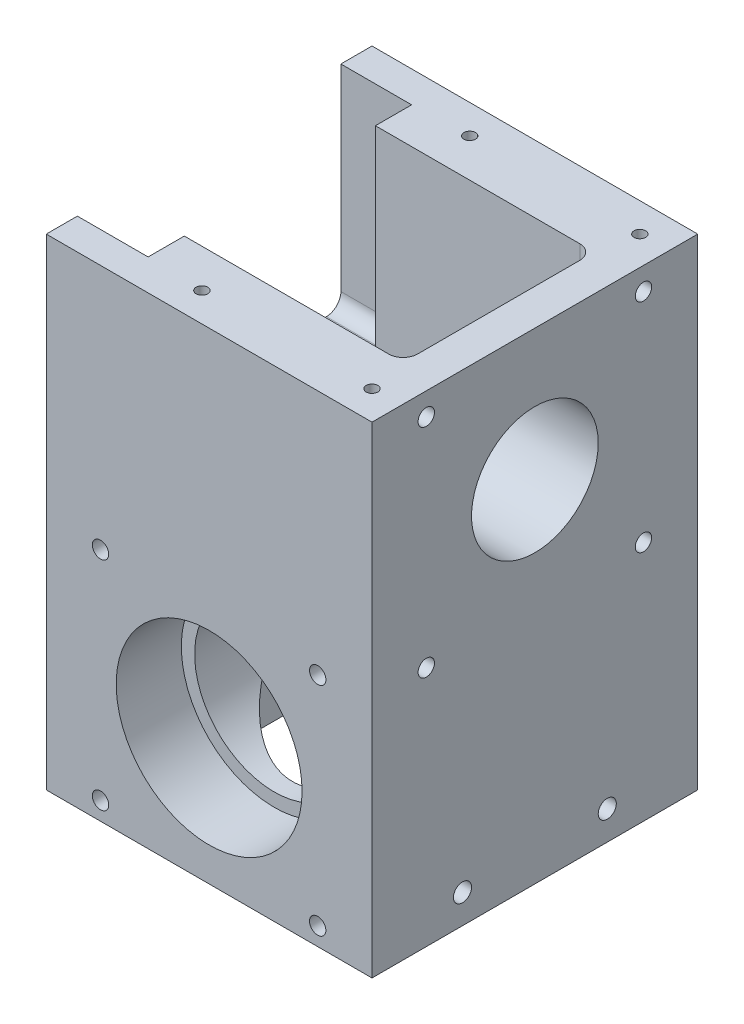
SolidWorks part; units mm, degrees
ref_plane "Front Plane" through (0, 0, 0) normal (0, 0, 1) x (1, 0, 0)
ref_plane "Top Plane" through (0, 0, 0) normal (0, 1, 0) x (1, 0, 0)
ref_plane "Right Plane" through (0, 0, 0) normal (1, 0, 0) x (0, 0, -1)
sketch "Sketch1" plane through (0, 0, 0) normal (0, 1, 0) x (1, 0, 0)
  line L1 (-22.5, -22.5) -> (22.5, -22.5)
  line L2 (-22.5, -22.5) -> (-22.5, 22.5)
  line L3 (-22.5, 22.5) -> (22.5, 22.5)
  line L4 (22.5, -22.5) -> (22.5, 22.5)
  line L5 (-22.5, -22.5) -> (22.5, 22.5) construction
  line L6 (-22.5, 22.5) -> (22.5, -22.5) construction
  point P0 (0, 0)
  dimension "D1" = 45
extrude "Boss-Extrude1" add sketch "Sketch1" along normal blind 30 and the other way blind 35
ref_plane "Plane1" through (0, 15, 0) normal (0, 1, 0) x (1, 0, 0)
ref_plane "Plane2" through (0, -17.5, 0) normal (0, -1, 0) x (-1, 0, 0)
hole_wizard "Ø22.0 (22) Diameter Hole1" positions "Sketch3" profile "Sketch4" hole size "Ø22.0" standard "DIN" end condition through all
sketch "Sketch3" plane through (0, 30, 0) normal (0, 1, 0) x (1, 0, 0)
  point P0 (0, 0)
sketch "Sketch4" plane through (0, 30, 0) normal (1, 0, 0) x (0, 0, 1)
  line L0 (0, 0) -> (0, 65)
  line L1 (0, 65) -> (11, 65)
  line L2 (11, 65) -> (11, 0)
  line L5 (11, 0) -> (0, 0)
  line L11 (0, -6.35) -> (0, 107.95) construction
  dimension "Thru Hole Dia." = 22
  dimension "Thru Hole Depth" = 65
hole_wizard "Ø22.0 (22) Diameter Hole2" positions "Sketch5" profile "Sketch6" hole size "Ø22.0" standard "DIN" end condition through all
sketch "Sketch5" plane through (0, 0, 22.5) normal (0, 0, 1) x (1, 0, 0)
  line L0 (-24.75, -17.5) -> (24.75, -17.5) construction
  point P0 (0, -17.5)
sketch "Sketch6" plane through (0, -17.5, 22.5) normal (1, 0, 0) x (0, -1, 0)
  line L0 (0, 0) -> (0, 45)
  line L1 (0, 45) -> (11, 45)
  line L2 (11, 45) -> (11, 0)
  line L5 (11, 0) -> (0, 0)
  line L11 (0, -6.35) -> (0, 107.95) construction
  dimension "Thru Hole Dia." = 22
  dimension "Thru Hole Depth" = 45
sketch "Sketch7" plane through (0, 0, 22.5) normal (0, 0, 1) x (1, 0, 0)
  circle A0 centre (0, -17.5) radius 12.8397
  dimension "D1" = 25.6794
extrude "Cut-Extrude1" cut sketch "Sketch7" against normal blind 9
cosmetic thread "Cosmetic Thread1" parameters "D1"=5, "D2"=26.289
sketch "Sketch8" plane through (0, 0, 0) normal (0, 0, 1) x (1, 0, 0)
  line L0 (-12.7279, 2.2721) -> (-11.9147, 1.4589)
  line L1 (-11.9147, 1.4589) -> (13.5411, 26.9147)
  line L2 (13.5411, 26.9147) -> (12.7279, 27.7279)
  line L3 (12.7279, 27.7279) -> (-12.7279, 2.2721)
  line L4 (24.75, 15) -> (-24.75, 15) construction
  point P2 (0, 15)
  dimension "D1" = 1.15
  dimension "D2" = 36
  dimension "D3" = 45
extrude "Cut-Extrude2" cut sketch "Sketch8" against normal mid plane 26.4
sketch "Sketch9" plane through (-6.6868, 6.6868, 0) normal (-0.7071, 0.7071, 0) x (0, 0, 1)
  line L4 (13.2, -7.3934) -> (13.2, 28.6066)
  line L5 (13.2, 28.6066) -> (-13.2, 28.6066)
  line L6 (-13.2, 28.6066) -> (-13.2, -7.3934)
  line L7 (-13.2, -7.3934) -> (13.2, -7.3934)
  line L8 (13.2, -7.3934) -> (13.2, 28.6066)
  line L9 (13.2, 28.6066) -> (-13.2, 28.6066)
  line L10 (-13.2, 28.6066) -> (-13.2, -7.3934)
  line L11 (-13.2, -7.3934) -> (13.2, -7.3934)
  dimension "D1" = 0
extrude "Cut-Extrude3" cut sketch "Sketch9" along normal up to next
fillet "Fillet1" radius 2 4 edges at (-17.2074, 6.7515, 13.2) (-17.2074, 6.7515, -13.2) (11.9985, 28.4574, 13.2) (11.9985, 28.4574, -13.2)
sketch "Sketch12" plane through (-6.6868, 6.6868, 0) normal (-0.7071, 0.7071, 0) x (0, 0, 1)
  line L0 (-11.2, -5.3934) -> (-11.2, -7.3934) construction
  line L1 (-9.2, -5.3934) -> (-9.2, -7.3934)
  line L2 (-13.2, -5.3934) -> (-13.2, -7.3934)
  line L4 (11.2, -5.3934) -> (11.2, -7.3934) construction
  line L5 (13.2, -5.3934) -> (13.2, -7.3934)
  line L6 (9.2, -5.3934) -> (9.2, -7.3934)
  line L7 (-11.2, -7.3934) -> (11.2, -7.3934) construction
  line L8 (-11.2, -7.3934) -> (11.2, -7.3934) construction
  arc A0 (-9.2, -5.3934) -> (-13.2, -5.3934) centre (-11.2, -5.3934) ccw
  arc A1 (-13.2, -7.3934) -> (-9.2, -7.3934) centre (-11.2, -7.3934) ccw
  arc A2 (13.2, -5.3934) -> (9.2, -5.3934) centre (11.2, -5.3934) ccw
  arc A3 (9.2, -7.3934) -> (13.2, -7.3934) centre (11.2, -7.3934) ccw
  point P2 (-11.2, -6.3934)
  point P7 (11.2, -6.3934)
  dimension "D1" = 2
extrude "Cut-Extrude6" cut sketch "Sketch12" along normal up to next
sketch "Sketch10" plane through (0, 30, 0) normal (0, 1, 0) x (1, 0, 0)
  line L6 (22.5, -22.5) -> (22.5, 22.5) construction
  line L7 (7.6274, 13.2) -> (15.5, 13.2)
  line L8 (7.6274, 13.2) -> (7.6274, -13.2)
  line L9 (7.6274, -13.2) -> (15.5, -13.2)
  line L10 (17.5, 11.2) -> (17.5, -11.2)
  arc A0 (15.5, -13.2) -> (17.5, -11.2) centre (15.5, -11.2) ccw
  arc A1 (15.5, 13.2) -> (17.5, 11.2) centre (15.5, 11.2) cw
  dimension "D1" = 2
  dimension "D2" = 5
extrude "Cut-Extrude4" cut sketch "Sketch10" against normal up to vertex (4.4995 mm away)
sketch "Sketch11" plane through (-22.5, 0, 0) normal (-1, 0, 0) x (0, 0, 1)
  line L0 (-22.5, 30) -> (-13.2, 30) construction
  line L1 (-18.2, 30) -> (18.2, 30)
  line L2 (-18.2, 30) -> (-18.2, 4.2721)
  line L3 (-16.2, 2.2721) -> (16.2, 2.2721)
  line L4 (18.2, 30) -> (18.2, 4.2721)
  arc A0 (16.2, 2.2721) -> (18.2, 4.2721) centre (16.2, 4.2721) ccw
  arc A1 (-18.2, 4.2721) -> (-16.2, 2.2721) centre (-16.2, 4.2721) ccw
  point P12 (18.2, 2.2721)
  point P15 (-18.2, 2.2721)
  dimension "D2" = 2
  dimension "D1" = 36.4
extrude "Cut-Extrude5" cut sketch "Sketch11" against normal up to vertex (9.7721 mm away) up to point (-12.7279, 2.2721, 0)
sketch "Sketch13" plane through (0, 0, 0) normal (1, 0, 0) x (0, 0, -1)
  line L0 (-17.5, -35) -> (22.5, 5)
  line L1 (-22.5, -35) -> (22.5, -35) construction
  line L2 (22.5, -35) -> (22.5, 30) construction
  line L3 (22.5, 5) -> (22.5, -35)
  line L4 (22.5, -35) -> (-17.5, -35)
  dimension "D1" = 40
extrude "Cut-Extrude7" cut sketch "Sketch13" against normal mid plane 30
sketch "Sketch18" plane through (0, 30, 0) normal (0, 1, 0) x (1, 0, 0)
  line L12 (-12.7279, -13.2) -> (-12.7279, -18.2)
  line L13 (-12.7279, -18.2) -> (-22.5, -18.2)
  line L14 (-22.5, -18.2) -> (-22.5, -22.5)
  line L15 (-22.5, -22.5) -> (22.5, -22.5)
  line L16 (22.5, -22.5) -> (22.5, 22.5)
  line L17 (22.5, 22.5) -> (-22.5, 22.5)
  line L18 (-22.5, 22.5) -> (-22.5, 18.2)
  line L19 (-22.5, 18.2) -> (-12.7279, 18.2)
  line L20 (-12.7279, 18.2) -> (-12.7279, 13.2)
  line L21 (-12.7279, 13.2) -> (15.5, 13.2)
  line L22 (17.5, 11.2) -> (17.5, -11.2)
  line L23 (15.5, -13.2) -> (-12.7279, -13.2)
  line L24 (-12.7279, -13.2) -> (-12.7279, -18.2)
  line L25 (-12.7279, -18.2) -> (-22.5, -18.2)
  line L26 (-22.5, -18.2) -> (-22.5, -22.5)
  line L27 (-22.5, -22.5) -> (22.5, -22.5)
  line L28 (22.5, -22.5) -> (22.5, 22.5)
  line L29 (22.5, 22.5) -> (-22.5, 22.5)
  line L30 (-22.5, 22.5) -> (-22.5, 18.2)
  line L31 (-22.5, 18.2) -> (-12.7279, 18.2)
  line L32 (-12.7279, 18.2) -> (-12.7279, 13.2)
  line L33 (-12.7279, 13.2) -> (15.5, 13.2)
  line L34 (17.5, 11.2) -> (17.5, -11.2)
  line L35 (15.5, -13.2) -> (-12.7279, -13.2)
  arc A2 (17.5, 11.2) -> (15.5, 13.2) centre (15.5, 11.2) ccw
  arc A3 (15.5, -13.2) -> (17.5, -11.2) centre (15.5, -11.2) ccw
  arc A4 (17.5, 11.2) -> (15.5, 13.2) centre (15.5, 11.2) ccw
  arc A5 (15.5, -13.2) -> (17.5, -11.2) centre (15.5, -11.2) ccw
  dimension "D1" = 0
extrude "Boss-Extrude2" add sketch "Sketch18" along normal blind 1.5
hole_wizard "M2 Tapped Hole1" positions "Sketch14" profile "Sketch15" tap size "M2" standard "DIN"
sketch "Sketch14" plane through (0, -8.75, -8.75) normal (0, -0.7071, -0.7071) x (-1, 0, 0)
  line L0 (15, -37.1231) -> (15, -8.8388) construction
  line L1 (15, -37.1231) -> (-15, -37.1231) construction
  point P0 (11.75, -28.1231)
  point P2 (11.75, 10.8769)
  point P4 (-11.75, 10.8769)
  point P6 (-11.75, -28.1231)
  dimension "D1" = 23.5
  dimension "D2" = 3.25
  dimension "D3" = 9
  dimension "D4" = 39
sketch "Sketch15" plane through (-11.75, -28.636, 11.136) normal (1, 0, 0) x (0, 0.7071, -0.7071)
  line L0 (0, 0) -> (0, 3.6807)
  line L1 (0, 3.6807) -> (0.8, 3.2)
  line L2 (0.8, 3.2) -> (0.8, 0)
  line L5 (0.8, 0) -> (0, 0)
  line L10 (0, 3.6807) -> (-0.8, 3.2) construction
  line L11 (0, -6.35) -> (0, 107.95) construction
  dimension "Tap Drill Dia." = 1.6
  dimension "Tap Drill Depth" = 3.2
  dimension "Drill Angle" = 118
cosmetic thread "Hole Thread1" parameters "D1"=2, "D2"=2
cosmetic thread "Hole Thread2" parameters "D1"=2, "D2"=2
cosmetic thread "Hole Thread3" parameters "D1"=2, "D2"=2
cosmetic thread "Hole Thread4" parameters "D1"=2, "D2"=2
hole_wizard "M2 Tapped Hole2" positions "Sketch16" profile "Sketch17" tap size "M2" standard "DIN"
sketch "Sketch16" plane through (0, 25.5005, 0) normal (0, 1, 0) x (1, 0, 0)
  line L2 (17.5, -11.2) -> (17.5, 11.2) construction
  line L4 (12.1269, -13.2) -> (15.5, -13.2) construction
  line L5 (15.5, 13.2) -> (12.1269, 13.2) construction
  point P0 (14.5, 7)
  point P2 (14.5, -7)
  dimension "D1" = 6.2
  dimension "D2" = 6.2
  dimension "D3" = 3
sketch "Sketch17" plane through (14.5, 25.5005, -7) normal (1, 0, 0) x (0, 0, 1)
  line L0 (0, 0) -> (0, 5.6807)
  line L1 (0, 5.6807) -> (0.8, 5.2)
  line L2 (0.8, 5.2) -> (0.8, 0)
  line L5 (0.8, 0) -> (0, 0)
  line L10 (0, 5.6807) -> (-0.8, 5.2) construction
  line L11 (0, -6.35) -> (0, 107.95) construction
  dimension "Tap Drill Dia." = 1.6
  dimension "Tap Drill Depth" = 5.2
  dimension "Drill Angle" = 118
cosmetic thread "Hole Thread5" parameters "D1"=4, "D2"=2
cosmetic thread "Hole Thread6" parameters "D1"=4, "D2"=2
hole_wizard "M2 Tapped Hole3" positions "Sketch20" profile "Sketch21" tap size "M2" standard "DIN"
sketch "Sketch20" plane through (0, 31.5, 0) normal (0, 1, 0) x (1, 0, 0)
  line L2 (22.5, 22.5) -> (-22.5, 22.5) construction
  line L3 (22.5, -22.5) -> (22.5, 22.5) construction
  line L4 (-22.5, -22.5) -> (22.5, -22.5) construction
  point P2 (-5, 18.5)
  point P4 (18.5, 18.5)
  point P8 (-5, -18.5)
  point P10 (18.5, -18.5)
  dimension "D1" = 4
  dimension "D2" = 5
  dimension "D3" = 4
  dimension "D4" = 4
sketch "Sketch21" plane through (-5, 31.5, -18.5) normal (1, 0, 0) x (0, 0, 1)
  line L0 (0, 0) -> (0, 5.6807)
  line L1 (0, 5.6807) -> (0.8, 5.2)
  line L2 (0.8, 5.2) -> (0.8, 0)
  line L5 (0.8, 0) -> (0, 0)
  line L10 (0, 5.6807) -> (-0.8, 5.2) construction
  line L11 (0, -6.35) -> (0, 107.95) construction
  dimension "Tap Drill Dia." = 1.6
  dimension "Tap Drill Depth" = 5.2
  dimension "Drill Angle" = 118
cosmetic thread "Hole Thread7" parameters "D1"=4, "D2"=2
cosmetic thread "Hole Thread8" parameters "D1"=4, "D2"=2
cosmetic thread "Hole Thread10" parameters "D1"=4, "D2"=2
cosmetic thread "Hole Thread11" parameters "D1"=4, "D2"=2
hole_wizard "M3 Tapped Hole1" positions "Sketch22" profile "Sketch23" tap size "M3" standard "DIN" end condition through all
sketch "Sketch22" plane through (-22.5, 0, 0) normal (-1, 0, 0) x (0, 0, 1)
  line L0 (-22.5, -35) -> (22.5, -35) construction
  point P0 (-10, -31)
  point P2 (10, -31)
  dimension "D1" = 10
  dimension "D2" = 10
  dimension "D3" = 4
sketch "Sketch23" plane through (-22.5, -31, -10) normal (0, 1, 0) x (0, 0, 1)
  line L0 (0, 0) -> (0, 45)
  line L1 (0, 45) -> (1.25, 45)
  line L2 (1.25, 45) -> (1.25, 0)
  line L5 (1.25, 0) -> (0, 0)
  line L11 (0, -6.35) -> (0, 107.95) construction
  dimension "Thru Tap Drill Dia." = 2.5
  dimension "Thru Tap Drill Depth" = 45
cosmetic thread "Hole Thread13" parameters "D2"=3
cosmetic thread "Hole Thread14" parameters "D2"=3
hole_wizard "M3 Tapped Hole2" positions "Sketch26" profile "Sketch27" tap size "M3" standard "DIN"
sketch "Sketch26" plane through (0, -35, 0) normal (0, -1, 0) x (-1, 0, 0)
  line L1 (19, 19) -> (-19, 19) construction
  line L2 (19, 19) -> (19, -19) construction
  line L3 (19, -19) -> (-19, -19) construction
  line L4 (-19, 19) -> (-19, -19) construction
  line L5 (19, 19) -> (-19, -19) construction
  line L6 (19, -19) -> (-19, 19) construction
  point P2 (-19, -19)
  point P61 (19, 19)
  point P62 (19, -19)
  point P63 (-19, 19)
  dimension "D1" = 38
sketch "Sketch27" plane through (19, -35, 19) normal (1, 0, 0) x (0, 0, -1)
  line L0 (0, 0) -> (0, 8.2511)
  line L1 (0, 8.2511) -> (1.25, 7.5)
  line L2 (1.25, 7.5) -> (1.25, 0)
  line L5 (1.25, 0) -> (0, 0)
  line L10 (0, 8.2511) -> (-1.25, 7.5) construction
  line L11 (0, -6.35) -> (0, 107.95) construction
  dimension "Tap Drill Dia." = 2.5
  dimension "Tap Drill Depth" = 7.5
  dimension "Drill Angle" = 118
cosmetic thread "Hole Thread15" parameters "D1"=6, "D2"=3
cosmetic thread "Hole Thread16" parameters "D1"=6, "D2"=3
cosmetic thread "Hole Thread17" parameters "D1"=6, "D2"=3
cosmetic thread "Hole Thread18" parameters "D1"=6, "D2"=3
hole_wizard "M2 Tapped Hole4" positions "Sketch28" profile "Sketch29" tap size "M2" standard "DIN"
sketch "Sketch28" plane through (-12.7279, 0, 0) normal (-1, 0, 0) x (0, 0, 1)
  line L0 (-18.2, 31.5) -> (-13.2, 31.5) construction
  line L1 (-13.2, 31.5) -> (-13.2, 2.2721) construction
  line L2 (13.2, 31.5) -> (13.2, 2.2721) construction
  point P0 (-14.7, 24)
  point P2 (14.7, 24)
  dimension "D1" = 7.5
  dimension "D2" = 1.5
  dimension "D3" = 1.5
sketch "Sketch29" plane through (-12.7279, 24, -14.7) normal (0, 1, 0) x (0, 0, 1)
  line L0 (0, 0) -> (0, 5.6807)
  line L1 (0, 5.6807) -> (0.8, 5.2)
  line L2 (0.8, 5.2) -> (0.8, 0)
  line L5 (0.8, 0) -> (0, 0)
  line L10 (0, 5.6807) -> (-0.8, 5.2) construction
  line L11 (0, -6.35) -> (0, 107.95) construction
  dimension "Tap Drill Dia." = 1.6
  dimension "Tap Drill Depth" = 5.2
  dimension "Drill Angle" = 118
cosmetic thread "Hole Thread19" parameters "D1"=4, "D2"=2
cosmetic thread "Hole Thread20" parameters "D1"=4, "D2"=2
sketch "Sketch30" plane through (22.5, 0, 0) normal (1, 0, 0) x (0, 0, -1)
  circle A0 centre (0, 13.3737) radius 8.75
  circle A1 centre (0, 13.3737) radius 11 construction
  dimension "D1" = 17.5
extrude "Cut-Extrude8" cut sketch "Sketch30" against normal up to surface (15.8339 mm away)
hole_wizard "#4-40 Tapped Hole1" positions "Sketch31" profile "Sketch32" tap size "#4-40" standard "ANSI Inch"
sketch "Sketch31" plane through (22.5, 0, 0) normal (1, 0, 0) x (0, 0, -1)
  circle A0 centre (0, 13.3737) radius 8.75 construction
  point P0 (-15, 28.3737)
  point P2 (-15, -1.6263)
  point P4 (15, -1.6263)
  point P6 (15, 28.3737)
  dimension "D1" = 15
  dimension "D2" = 30
  dimension "D3" = 30
  dimension "D4" = 15
sketch "Sketch32" plane through (22.5, 28.3737, 15) normal (0, 1, 0) x (0, 0, -1)
  line L0 (0, 0) -> (0, 4.8792)
  line L1 (0, 4.8792) -> (1.1303, 4.2)
  line L2 (1.1303, 4.2) -> (1.1303, 0)
  line L5 (1.1303, 0) -> (0, 0)
  line L10 (0, 4.8792) -> (-1.1303, 4.2) construction
  line L11 (0, -6.35) -> (0, 107.95) construction
  dimension "Tap Drill Dia." = 2.2606
  dimension "Tap Drill Depth" = 4.2
  dimension "Drill Angle" = 118
cosmetic thread "Hole Thread21" parameters "D1"=2, "D2"=2.8448
cosmetic thread "Hole Thread22" parameters "D1"=2, "D2"=2.8448
cosmetic thread "Hole Thread23" parameters "D1"=2, "D2"=2.8448
cosmetic thread "Hole Thread24" parameters "D1"=2, "D2"=2.8448
hole_wizard "#4-40 Tapped Hole2" positions "Sketch34" profile "Sketch35" tap size "#4-40" standard "ANSI Inch"
sketch "Sketch34" plane through (0, 0, 22.5) normal (0, 0, 1) x (1, 0, 0)
  line L1 (-15, -32.5) -> (15, -32.5) construction
  line L2 (-15, -32.5) -> (-15, -2.5) construction
  line L3 (-15, -2.5) -> (15, -2.5) construction
  line L4 (15, -32.5) -> (15, -2.5) construction
  line L5 (-15, -32.5) -> (15, -2.5) construction
  line L6 (-15, -2.5) -> (15, -32.5) construction
  circle A0 centre (0, -17.5) radius 11 construction
  point P0 (-15, -2.5)
  point P2 (15, -2.5)
  point P4 (-15, -32.5)
  point P6 (15, -32.5)
  point P84 (0, -17.5)
  dimension "D1" = 30
sketch "Sketch35" plane through (-15, -2.5, 22.5) normal (1, 0, 0) x (0, -1, 0)
  line L0 (0, 0) -> (0, 5.8592)
  line L1 (0, 5.8592) -> (1.1303, 5.18)
  line L2 (1.1303, 5.18) -> (1.1303, 0)
  line L5 (1.1303, 0) -> (0, 0)
  line L10 (0, 5.8592) -> (-1.1303, 5.18) construction
  line L11 (0, -6.35) -> (0, 107.95) construction
  dimension "Tap Drill Dia." = 2.2606
  dimension "Tap Drill Depth" = 5.18
  dimension "Drill Angle" = 118
cosmetic thread "Hole Thread25" parameters "D1"=2, "D2"=2.8448
cosmetic thread "Hole Thread26" parameters "D1"=2, "D2"=2.8448
cosmetic thread "Hole Thread27" parameters "D1"=2, "D2"=2.8448
cosmetic thread "Hole Thread28" parameters "D1"=2, "D2"=2.8448
